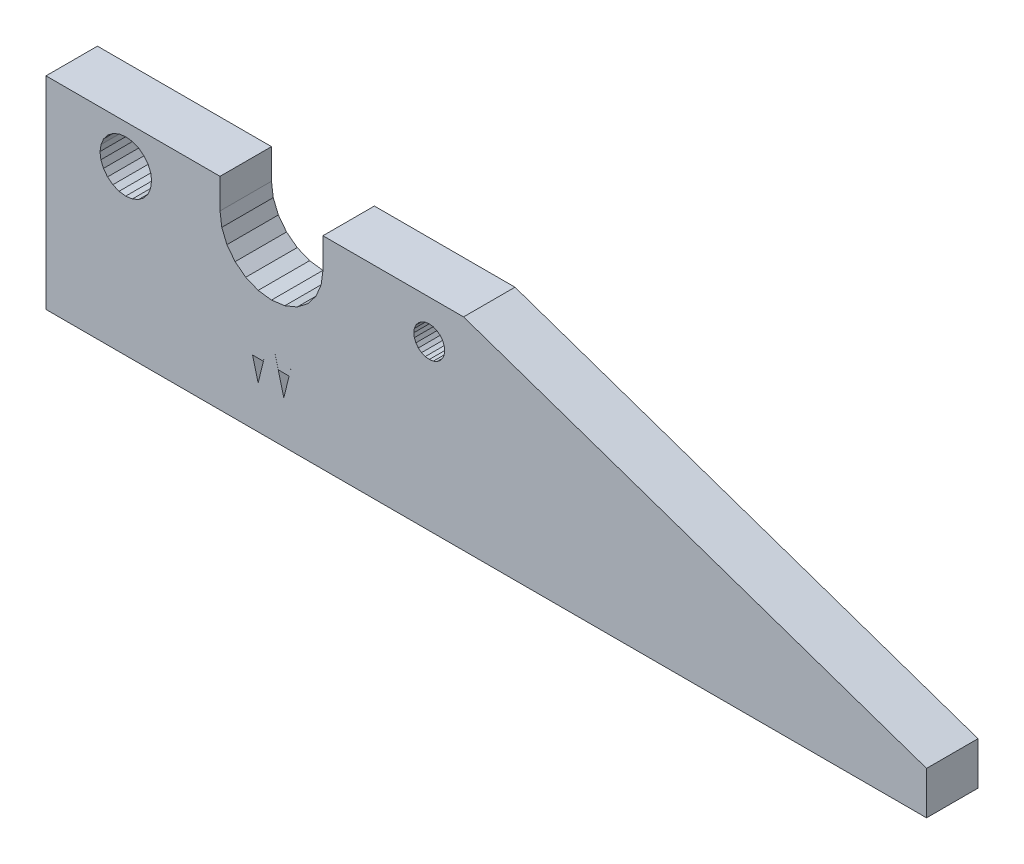
SolidWorks part; units mm, degrees
material "Maple"
ref_plane "Front Plane" through (0, 0, 0) normal (0, 0, 1) x (1, 0, 0)
ref_plane "Top Plane" through (0, 0, 0) normal (0, 1, 0) x (1, 0, 0)
ref_plane "Right Plane" through (0, 0, 0) normal (1, 0, 0) x (0, 0, -1)
sketch "Sketch1" plane through (0, 0, 0) normal (0, 0, 1) x (1, 0, 0)
  line L2190 (-380.6981, -270.3658) -> (-382.1452, -269.7664)
  line L2191 (-383.3878, -268.8129) -> (-384.3413, -267.5703)
  line L2192 (-359.8452, -267.1291) -> (-360.2793, -267.3089)
  line L2193 (-397.6204, -262.9722) -> (-396.8968, -262.6725)
  line L2194 (-399.0429, -266.3467) -> (-399.1452, -265.5703)
  line L2195 (-396.1452, -268.5703) -> (-396.9216, -268.4681)
  line L2196 (-360.7452, -263.7703) -> (-360.2793, -263.8316)
  line L2197 (-361.211, -263.8316) -> (-360.7452, -263.7703)
  line L2198 (-361.6452, -264.0114) -> (-361.211, -263.8316)
  line L2199 (-362.0179, -264.2975) -> (-361.6452, -264.0114)
  line L2200 (-362.304, -264.6703) -> (-362.0179, -264.2975)
  line L2201 (-362.4838, -265.1044) -> (-362.304, -264.6703)
  line L2202 (-362.4838, -266.0362) -> (-362.5452, -265.5703)
  line L2203 (-362.304, -266.4703) -> (-362.4838, -266.0362)
  line L2204 (-361.6452, -267.1291) -> (-362.0179, -266.8431)
  line L2205 (-361.211, -267.3089) -> (-361.6452, -267.1291)
  line L2206 (-398.2665, -267.6916) -> (-398.7432, -267.0703)
  line L2207 (-359.1863, -266.4703) -> (-359.4724, -266.8431)
  line L2208 (-359.0065, -266.0362) -> (-359.1863, -266.4703)
  line L2209 (-358.9452, -265.5703) -> (-359.0065, -266.0362)
  line L2210 (-359.0065, -265.1044) -> (-358.9452, -265.5703)
  line L2211 (-359.1863, -264.6703) -> (-359.0065, -265.1044)
  line L2212 (-359.4724, -264.2975) -> (-359.1863, -264.6703)
  line L2213 (-405.4434, -261.0703) -> (-405.4434, -284.6703)
  line L2214 (-362.5452, -265.5703) -> (-362.4838, -265.1044)
  line L2215 (-362.0179, -266.8431) -> (-362.304, -266.4703)
  line L2216 (-359.8452, -264.0114) -> (-359.4724, -264.2975)
  line L2217 (-360.2793, -263.8316) -> (-359.8452, -264.0114)
  line L2218 (-373.1452, -261.0703) -> (-356.7452, -261.0703)
  line L2219 (-405.4434, -261.0703) -> (-385.1452, -261.0703)
  line L2220 (-394.6452, -268.1684) -> (-395.3687, -268.4681)
  line L2221 (-395.3687, -268.4681) -> (-396.1452, -268.5703)
  line L2222 (-393.5471, -267.0703) -> (-394.0238, -267.6916)
  line L2223 (-393.2474, -266.3467) -> (-393.5471, -267.0703)
  line L2224 (-385.1452, -264.5703) -> (-385.1452, -261.0703)
  line L2225 (-384.9407, -266.1232) -> (-385.1452, -264.5703)
  line L2226 (-394.6204, -262.9722) -> (-393.999, -263.449)
  line L2227 (-398.7432, -267.0703) -> (-399.0429, -266.3467)
  line L2228 (-394.0238, -267.6916) -> (-394.6452, -268.1684)
  line L2229 (-396.9216, -268.4681) -> (-397.6452, -268.1684)
  line L2230 (-393.1452, -265.5703) -> (-393.2474, -266.3467)
  line L2231 (-393.5223, -264.0703) -> (-393.2226, -264.7938)
  line L2232 (-396.1204, -262.5703) -> (-395.3439, -262.6725)
  line L2233 (-399.0181, -264.7938) -> (-398.7184, -264.0703)
  line L2234 (-398.7184, -264.0703) -> (-398.2417, -263.449)
  line L2235 (-398.2417, -263.449) -> (-397.6204, -262.9722)
  line L2236 (-397.6452, -268.1684) -> (-398.2665, -267.6916)
  line L2237 (-405.4434, -284.6703) -> (-302.7452, -284.6703)
  line L2238 (-302.7452, -284.6703) -> (-302.7452, -279.6703)
  line L2239 (-302.7452, -279.6703) -> (-356.7452, -261.0703)
  line L2240 (-399.1452, -265.5703) -> (-399.0181, -264.7938)
  line L2241 (-393.2226, -264.7938) -> (-393.1452, -265.3819)
  line L2242 (-360.7452, -267.3703) -> (-361.211, -267.3089)
  line L2243 (-360.2793, -267.3089) -> (-360.7452, -267.3703)
  line L2244 (-359.4724, -266.8431) -> (-359.8452, -267.1291)
  line L2245 (-395.3439, -262.6725) -> (-394.6204, -262.9722)
  line L2246 (-373.1452, -264.5703) -> (-373.1452, -261.0703)
  line L2247 (-373.1452, -264.5703) -> (-373.3496, -266.1232)
  line L2248 (-373.3496, -266.1232) -> (-373.949, -267.5703)
  line L2249 (-373.949, -267.5703) -> (-374.9025, -268.8129)
  line L2250 (-374.9025, -268.8129) -> (-376.1452, -269.7664)
  line L2251 (-376.1452, -269.7664) -> (-377.5922, -270.3658)
  line L2252 (-377.5922, -270.3658) -> (-379.1452, -270.5703)
  line L2253 (-379.1452, -270.5703) -> (-380.6981, -270.3658)
  line L2254 (-382.1452, -269.7664) -> (-383.3878, -268.8129)
  line L2255 (-384.3413, -267.5703) -> (-384.9407, -266.1232)
  line L2256 (-393.999, -263.449) -> (-393.5223, -264.0703)
  line L2257 (-393.1452, -265.3819) -> (-393.1452, -265.5703)
  line L2258 (-396.8968, -262.6725) -> (-396.1204, -262.5703)
  line L8893 (-377.0935, -277.225) -> (-377.7054, -279.7164)
  line L8894 (-377.7054, -279.7164) -> (-378.3548, -277.225)
  line L8895 (-378.3548, -277.225) -> (-377.0935, -277.225)
  line L8896 (-378.8293, -275.4023) -> (-377.7054, -279.7164)
  line L8897 (-377.7054, -279.7164) -> (-376.644, -275.4023)
  line L8898 (-376.644, -275.4023) -> (-377.0935, -277.2193)
  line L8899 (-377.0935, -277.2193) -> (-378.3548, -277.2193)
  line L8900 (-378.3548, -277.2193) -> (-378.8293, -275.4023)
  line L8901 (-380.0905, -277.225) -> (-380.7024, -279.7164)
  line L8902 (-380.7024, -279.7164) -> (-381.3517, -277.225)
  line L8903 (-381.3517, -277.225) -> (-380.0905, -277.225)
  line L8904 (-381.8263, -275.4023) -> (-380.7024, -279.7164)
  line L8905 (-380.7024, -279.7164) -> (-379.6409, -275.4023)
  line L8906 (-379.6409, -275.4023) -> (-380.0905, -277.2193)
  line L8907 (-380.0905, -277.2193) -> (-381.3517, -277.2193)
  line L8908 (-381.3517, -277.2193) -> (-381.8263, -275.4023)
extrude "Boss-Extrude1" add sketch "Sketch1" along normal blind 6 contours L2191 L2255 L2225 L2224 L2219 L2213 L2237 L2238 L2239 L2218 L2246 L2247 L2248 L2249 L2250 L2251 L2252 L2253 L2190 L2254 L8908 L8907 L8906 L8905 L8902 L8903 L8904 L2207 L2244 L2192 L2243 L2242 L2205 L2204 L2215 L2203 L2202 L2214 L2201 L2200 L2199 L2198 L2197 L2196 L2217 L2216 L2212 L2211 L2210
